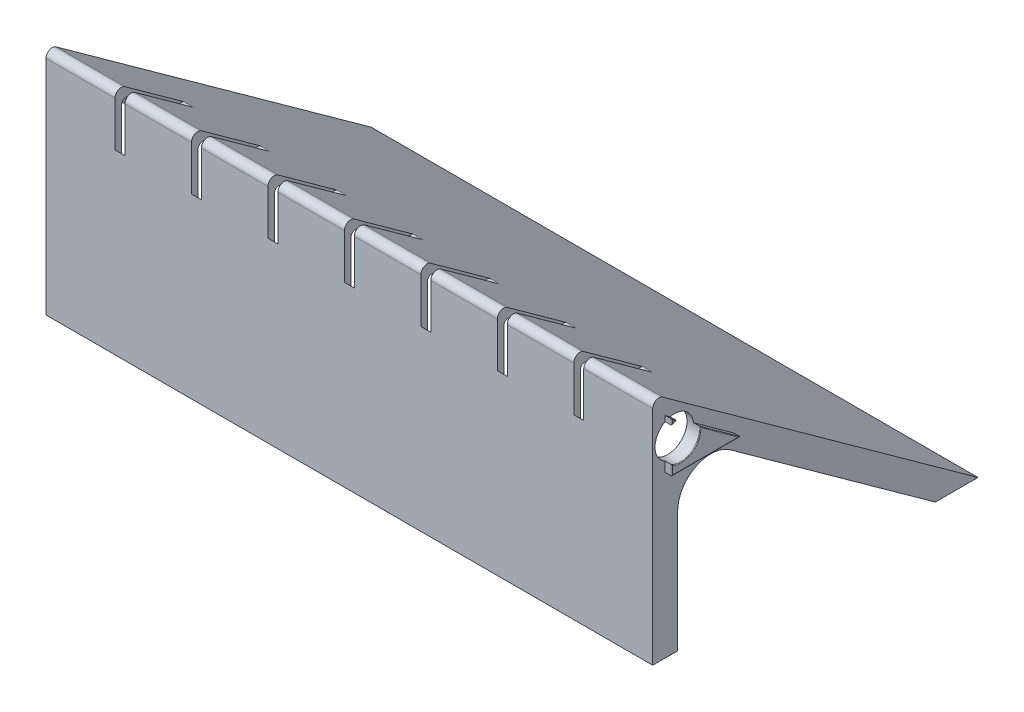
SolidWorks part; units mm, degrees
ref_plane "Front Plane" through (0, 0, 0) normal (0, 0, 1) x (1, 0, 0)
ref_plane "Top Plane" through (0, 0, 0) normal (0, 1, 0) x (1, 0, 0)
ref_plane "Right Plane" through (0, 0, 0) normal (1, 0, 0) x (0, 0, -1)
sketch "Sketch1" plane through (0, 0, 0) normal (1, 0, 0) x (0, 0, -1)
  line L0 (0, 0) -> (0, 84.9016)
  line L1 (3.7734, 86.8335) -> (124.2686, 0)
  line L2 (124.2686, 0) -> (107.9767, 0)
  line L3 (0, 0) -> (0, 120.65) construction
  line L4 (132.4146, 0) -> (135.763, -2.413) construction
  line L5 (107.9767, 0) -> (29.65, 56.4453)
  line L6 (9.525, 46.1419) -> (9.525, 0)
  line L7 (9.525, 0) -> (0, 0)
  arc A0 (0, 84.9016) -> (3.7734, 86.8335) centre (2.3813, 84.9016) cw
  arc A1 (29.65, 56.4453) -> (9.525, 46.1419) centre (22.225, 46.1419) ccw
  dimension "D3" = 2.3813
  dimension "D6" = 12.7
  dimension "D1" = 120.65
  dimension "D2" = 4.7625
  dimension "D4" = 9.525
  dimension "D5" = 9.525
extrude "Boss-Extrude1" add sketch "Sketch1" along normal mid plane 231.775
shell "Shell1" thickness 2.54
fillet "Fillet7" radius 1.5875 1 edges at (0, 84.5916, -2.54)
fillet "Fillet6" radius 3.175 1 edges at (0, 2.54, -116.3995)
sketch "Sketch3" plane through (0, -2.413, -15.875) normal (-1, 0, 0) x (0, 0, 1)
  line L2 (-7.7959, 75.4997) -> (17.0233, 93.0233) construction
  line L3 (17.0233, 75.1021) -> (15.4906, 70.651) construction
  line L4 (-7.3725, 71.2621) -> (-7.7215, 70.7777) construction
  line L5 (-7.9267, 71.3619) -> (-8.2712, 70.8839)
  line L6 (17.0233, 93.0233) -> (17.0233, 75.1021) construction
  line L7 (17.5313, 75.0171) -> (15.971, 70.4856)
  line L8 (17.5313, 94.0038) -> (17.5313, 75.0171)
  line L9 (-8.2811, 75.779) -> (17.5313, 94.0038)
  arc A1 (-7.7959, 75.4997) -> (-7.3725, 71.2621) centre (4.1553, 74.5541) ccw construction
  arc A2 (15.3478, 70.2585) -> (15.4906, 70.651) centre (4.1553, 74.5541) ccw construction
  arc A3 (-8.2811, 75.779) -> (-7.9267, 71.3619) centre (4.1553, 74.5541) ccw
  arc A4 (-8.2712, 70.8839) -> (15.8283, 70.0928) centre (3.8865, 73.7745) ccw
  arc A5 (15.8283, 70.0928) -> (15.971, 70.4856) centre (4.1553, 74.5541) ccw
  arc A10 (-7.7215, 70.7777) -> (15.3478, 70.2585) centre (3.8865, 73.7745) ccw construction
  dimension "D1" = 0.508
extrude "Cut-Extrude1" cut sketch "Sketch3" against normal mid plane 3.81
fillet "Fillet8" radius 1.5875 1 edges at (0, 72.1017, -24.2162)
pattern_linear "LPattern1" count 4 spacing 29.21 along (1, 0, 0) of "Cut-Extrude1", "Fillet8"
pattern_linear "LPattern2" count 4 spacing 29.21 along (-1, 0, 0) of "Cut-Extrude1", "Fillet8"
sketch "Sketch4" plane through (115.8875, 0, 0) normal (1, 0, 0) x (0, 0, -1)
  line L0 (4.7625, 80.2505) -> (4.7625, 78.1879)
  line L1 (4.7625, 119.8563) -> (4.7625, 0.7938) construction
  line L2 (4.7625, 80.2505) -> (6.6487, 78.8912)
  line L3 (4.7625, 80.2505) -> (116.1227, 0) construction
  line L4 (30.8726, 61.4345) -> (15.6087, 72.4343)
  line L5 (30.8726, 61.4345) -> (4.7625, 61.4345)
  line L6 (4.7625, 61.4345) -> (4.7625, 65.1812)
  line L9 (37.2955, 61.4345) -> (0.058, 61.4345) construction
  arc A0 (4.7625, 65.1812) -> (15.6087, 72.4343) centre (8.2618, 71.6845) ccw
  arc A1 (14.843, 73.1845) -> (14.843, 70.1845) centre (8.2618, 71.6845) ccw construction
  arc A2 (6.6487, 78.8912) -> (4.7625, 78.1879) centre (8.2618, 71.6845) ccw
  dimension "D1" = 0.635
extrude "Boss-Extrude2" add sketch "Sketch4" along normal up to vertex (2.54 mm away)
sketch "Sketch5" plane through (115.8875, 0, 0) normal (1, 0, 0) x (0, 0, -1)
  circle A0 centre (8.2618, 71.6845) radius 7.385
  arc A3 (4.7625, 65.1812) -> (15.6087, 72.4343) centre (8.2618, 71.6845) ccw construction
extrude "Cut-Extrude2" cut sketch "Sketch5" against normal blind 4.8
fillet "Fillet4" radius 0.254 3 edges at (118.4275, 78.6041, -5.6815) (118.4275, 79.2192, -4.7625) (118.4275, 79.5708, -5.7056)
fillet "Fillet5" radius 0.254 4 edges at (118.4275, 63.3079, -4.7625) (118.4275, 65.5457, -12.367) (118.4275, 66.9344, -23.2406) (118.4275, 61.4345, -17.8175)
sketch "Sketch6" plane through (-113.3475, 0, 0) normal (1, 0, 0) x (0, 0, -1)
  circle A0 centre (8.2618, 71.6845) radius 3.2385
  dimension "D1" = 6.477
extrude "Cut-Extrude3" cut sketch "Sketch6" against normal through all
